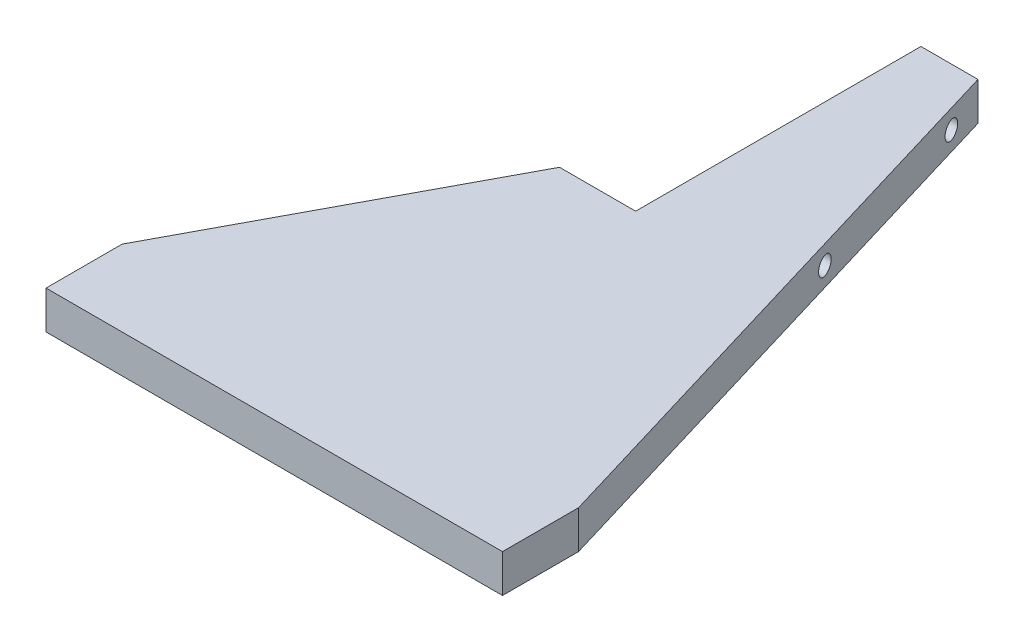
SolidWorks part; units mm, degrees
ref_plane "Front Plane" through (0, 0, 0) normal (0, 0, 1) x (1, 0, 0)
ref_plane "Top Plane" through (0, 0, 0) normal (0, 1, 0) x (1, 0, 0)
ref_plane "Right Plane" through (0, 0, 0) normal (1, 0, 0) x (0, 0, -1)
sketch "Sketch1" plane through (0, 0, 0) normal (0, 1, 0) x (1, 0, 0)
  line L0 (0, 0) -> (0, 12.7)
  line L1 (0, 12.7) -> (25.4, 60.325)
  line L2 (25.4, 60.325) -> (38.1, 60.325)
  line L3 (38.1, 60.325) -> (38.1, 107.95)
  line L4 (38.1, 107.95) -> (47.625, 107.95)
  line L5 (47.625, 107.95) -> (76.2, 12.7)
  line L6 (76.2, 12.7) -> (76.2, 0)
  line L7 (0, 0) -> (76.2, 0)
  point P12 (38.1, 0)
  dimension "D1" = 9.525
  dimension "D2" = 107.95
  dimension "D3" = 12.7
  dimension "D4" = 47.625
  dimension "D5" = 12.7
  dimension "D6" = 76.2
extrude "Boss-Extrude1" add sketch "Sketch1" along normal blind 6.35 contours L1 L2 L3 L4 L5 L6 L7 L0
sketch "Sketch2" plane through (38.1, 0, 0) normal (-1, 0, 0) x (0, 0, 1)
  line L1 (-107.95, 6.35) -> (-107.95, 0) construction
  line L2 (-60.325, 6.35) -> (-60.325, 0) construction
  circle A0 centre (-101.6, 3.175) radius 1.5
  circle A1 centre (-71.4375, 3.175) radius 1.5
  point P8 (-107.95, 3.175)
  dimension "D3" = 3
  dimension "D1" = 6.35
  dimension "D2" = 11.1125
extrude "Cut-Extrude1" cut sketch "Sketch2" against normal through all both and the other way through all
